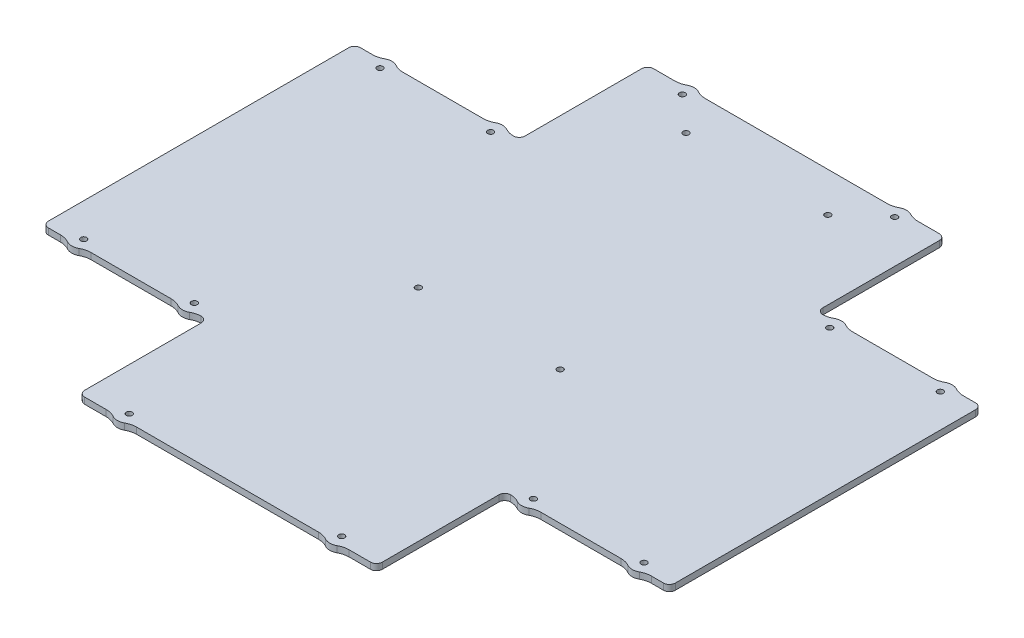
SolidWorks part; units mm, degrees
ref_plane "Front Plane" through (0, 0, 0) normal (0, 0, 1) x (1, 0, 0)
ref_plane "Top Plane" through (0, 0, 0) normal (0, 1, 0) x (1, 0, 0)
ref_plane "Right Plane" through (0, 0, 0) normal (1, 0, 0) x (0, 0, -1)
ref_plane "Plane1" through (0, 3.175, 0) normal (0, 1, 0) x (1, 0, 0)
sketch "Sketch1" plane through (0, 3.175, 0) normal (0, 1, 0) x (1, 0, 0)
  line L0 (93.596, -79) -> (134.104, -79)
  line L1 (149.596, -79) -> (155.7, -79)
  line L2 (158.7, -76) -> (158.7, 76)
  line L3 (155.7, 79) -> (149.596, 79)
  line L4 (134.104, 79) -> (93.596, 79)
  line L5 (75.35, 82) -> (75.35, 141)
  line L6 (72.35, 144) -> (61.496, 144)
  line L7 (46.004, 144) -> (-46.004, 144)
  line L8 (-61.496, 144) -> (-72.35, 144)
  line L9 (-75.35, 141) -> (-75.35, 82)
  line L10 (-93.596, 79) -> (-134.104, 79)
  line L11 (-149.596, 79) -> (-155.7, 79)
  line L12 (-158.7, 76) -> (-158.7, -76)
  line L13 (-155.7, -79) -> (-149.596, -79)
  line L14 (-134.104, -79) -> (-93.596, -79)
  line L15 (-75.35, -82) -> (-75.35, -141)
  line L16 (-72.35, -144) -> (-61.496, -144)
  line L17 (-46.004, -144) -> (46.004, -144)
  line L18 (61.496, -144) -> (72.35, -144)
  line L19 (75.35, -141) -> (75.35, -82)
  circle A0 centre (141.85, -75) radius 1.5
  circle A1 centre (85.85, -75) radius 1.5
  circle A2 centre (53.75, -140) radius 1.5
  circle A3 centre (-53.75, -140) radius 1.5
  circle A4 centre (-85.85, -75) radius 1.5
  circle A5 centre (-141.85, -75) radius 1.5
  circle A6 centre (141.85, 75) radius 1.5
  circle A7 centre (85.85, 75) radius 1.5
  circle A8 centre (53.75, 140) radius 1.5
  circle A9 centre (-53.75, 140) radius 1.5
  circle A10 centre (-85.85, 75) radius 1.5
  circle A11 centre (-141.85, 75) radius 1.5
  circle A12 centre (-35.9, 124) radius 1.5
  circle A13 centre (35.9, 124) radius 1.5
  circle A14 centre (-35.9, -11.5) radius 1.5
  circle A15 centre (35.9, -11.5) radius 1.5
  arc A16 (82.9431, -80.2488) -> (88.7547, -80.25) centre (85.85, -75) ccw
  arc A17 (88.7547, -80.25) -> (93.596, -79) centre (93.596, -89) cw
  arc A18 (134.104, -79) -> (138.9453, -80.25) centre (134.104, -89) cw
  arc A19 (138.9453, -80.25) -> (144.7547, -80.25) centre (141.85, -75) ccw
  arc A20 (144.7547, -80.25) -> (149.596, -79) centre (149.596, -89) cw
  arc A21 (155.7, -79) -> (158.7, -76) centre (155.7, -76) ccw
  arc A22 (158.7, 76) -> (155.7, 79) centre (155.7, 76) ccw
  arc A23 (149.596, 79) -> (144.7547, 80.25) centre (149.596, 89) cw
  arc A24 (144.7547, 80.25) -> (138.9453, 80.25) centre (141.85, 75) ccw
  arc A25 (138.9453, 80.25) -> (134.104, 79) centre (134.104, 89) cw
  arc A26 (93.596, 79) -> (88.7547, 80.25) centre (93.596, 89) cw
  arc A27 (88.7547, 80.25) -> (82.9431, 80.2488) centre (85.85, 75) ccw
  arc A28 (82.9431, 80.2488) -> (78.35, 79) centre (78.0983, 88.9968) cw
  arc A29 (78.35, 79) -> (75.35, 82) centre (78.35, 82) cw
  arc A30 (75.35, 141) -> (72.35, 144) centre (72.35, 141) ccw
  arc A31 (61.496, 144) -> (56.6547, 145.25) centre (61.496, 154) cw
  arc A32 (56.6547, 145.25) -> (50.8453, 145.25) centre (53.75, 140) ccw
  arc A33 (50.8453, 145.25) -> (46.004, 144) centre (46.004, 154) cw
  arc A34 (-46.004, 144) -> (-50.8453, 145.25) centre (-46.004, 154) cw
  arc A35 (-50.8453, 145.25) -> (-56.6547, 145.25) centre (-53.75, 140) ccw
  arc A36 (-56.6547, 145.25) -> (-61.496, 144) centre (-61.496, 154) cw
  arc A37 (-72.35, 144) -> (-75.35, 141) centre (-72.35, 141) ccw
  arc A38 (-75.35, 82) -> (-78.35, 79) centre (-78.35, 82) cw
  arc A39 (-78.35, 79) -> (-82.9431, 80.2488) centre (-78.0983, 88.9968) cw
  arc A40 (-82.9431, 80.2488) -> (-88.7547, 80.25) centre (-85.85, 75) ccw
  arc A41 (-88.7547, 80.25) -> (-93.596, 79) centre (-93.596, 89) cw
  arc A42 (-134.104, 79) -> (-138.9453, 80.25) centre (-134.104, 89) cw
  arc A43 (-138.9453, 80.25) -> (-144.7547, 80.25) centre (-141.85, 75) ccw
  arc A44 (-144.7547, 80.25) -> (-149.596, 79) centre (-149.596, 89) cw
  arc A45 (-155.7, 79) -> (-158.7, 76) centre (-155.7, 76) ccw
  arc A46 (-158.7, -76) -> (-155.7, -79) centre (-155.7, -76) ccw
  arc A47 (-149.596, -79) -> (-144.7547, -80.25) centre (-149.596, -89) cw
  arc A48 (-144.7547, -80.25) -> (-138.9453, -80.25) centre (-141.85, -75) ccw
  arc A49 (-138.9453, -80.25) -> (-134.104, -79) centre (-134.104, -89) cw
  arc A50 (-93.596, -79) -> (-88.7547, -80.25) centre (-93.596, -89) cw
  arc A51 (-88.7547, -80.25) -> (-82.9431, -80.2488) centre (-85.85, -75) ccw
  arc A52 (-82.9431, -80.2488) -> (-78.35, -79) centre (-78.0983, -88.9968) cw
  arc A53 (-78.35, -79) -> (-75.35, -82) centre (-78.35, -82) cw
  arc A54 (-75.35, -141) -> (-72.35, -144) centre (-72.35, -141) ccw
  arc A55 (-61.496, -144) -> (-56.6547, -145.25) centre (-61.496, -154) cw
  arc A56 (-56.6547, -145.25) -> (-50.8453, -145.25) centre (-53.75, -140) ccw
  arc A57 (-50.8453, -145.25) -> (-46.004, -144) centre (-46.004, -154) cw
  arc A58 (46.004, -144) -> (50.8453, -145.25) centre (46.004, -154) cw
  arc A59 (50.8453, -145.25) -> (56.6547, -145.25) centre (53.75, -140) ccw
  arc A60 (56.6547, -145.25) -> (61.496, -144) centre (61.496, -154) cw
  arc A61 (72.35, -144) -> (75.35, -141) centre (72.35, -141) ccw
  arc A62 (75.35, -82) -> (78.35, -79) centre (78.35, -82) cw
  arc A63 (78.35, -79) -> (82.9431, -80.2488) centre (78.0983, -88.9968) cw
extrude "Boss-Extrude1" add sketch "Sketch1" against normal blind 3.175
